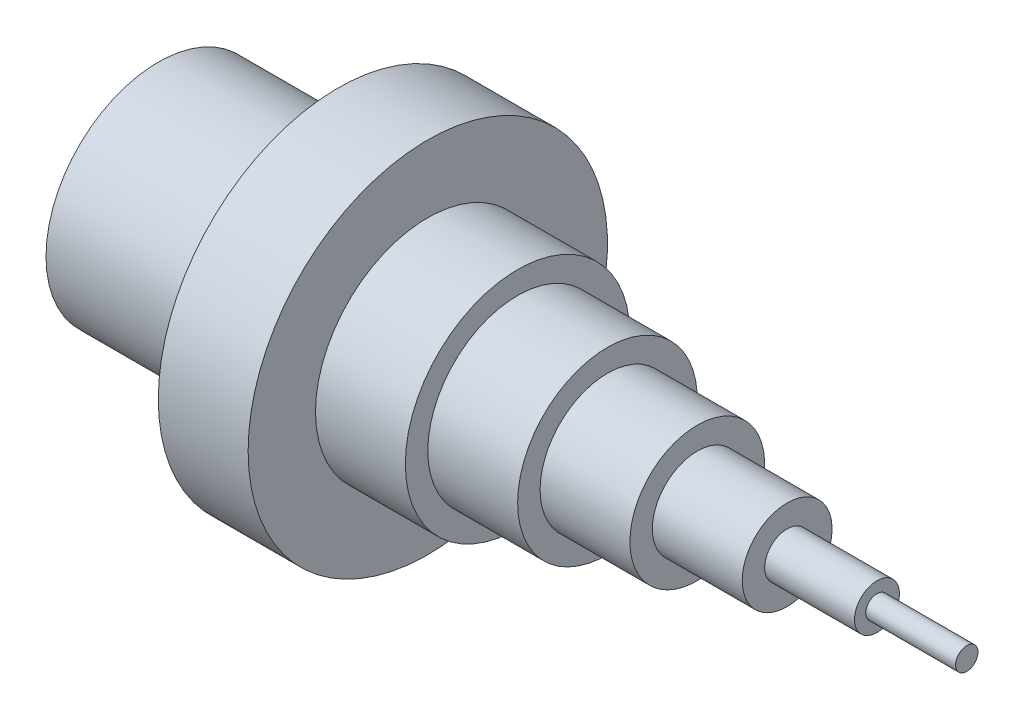
SolidWorks part; units mm, degrees
ref_plane "Front Plane" through (0, 0, 0) normal (0, 0, 1) x (1, 0, 0)
ref_plane "Top Plane" through (0, 0, 0) normal (0, 1, 0) x (1, 0, 0)
ref_plane "Right Plane" through (0, 0, 0) normal (1, 0, 0) x (0, 0, -1)
sketch "Sketch2" plane through (0, 0, 0) normal (0, 1, 0) x (1, 0, 0)
  line L0 (0, 0) -> (183.4043, 0) construction
  line L1 (0, 0) -> (0, -25)
  line L2 (0, -25) -> (40, -25)
  line L3 (40, -25) -> (40, -40)
  line L4 (40, -40) -> (60, -40)
  line L5 (60, -40) -> (60, -25)
  line L6 (60, -25) -> (80, -25)
  line L7 (80, -25) -> (80, -20)
  line L8 (80, -20) -> (100, -20)
  line L9 (100, -20) -> (100, -15)
  line L10 (100, -15) -> (120, -15)
  line L11 (120, -15) -> (120, -10)
  line L12 (120, -10) -> (140, -10)
  line L13 (140, -10) -> (140, -5)
  line L14 (140, -5) -> (160, -5)
  line L15 (160, -5) -> (160, -2.5)
  line L16 (160, -2.5) -> (180, -2.5)
  line L17 (180, -2.5) -> (180, 0)
  line L18 (0, 0) -> (180, 0)
  dimension "D1" = 20
  dimension "D2" = 20
  dimension "D3" = 20
  dimension "D4" = 20
  dimension "D5" = 20
  dimension "D6" = 20
  dimension "D7" = 20
  dimension "D8" = 5
  dimension "D9" = 10
  dimension "D10" = 20
  dimension "D11" = 30
  dimension "D12" = 40
  dimension "D13" = 50
  dimension "D14" = 50
  dimension "D15" = 80
  dimension "D16" = 40
revolve "Revolve1" add sketch "Sketch2" angle 360 about L0
sketch "Sketch3" plane through (0, 0, 0) normal (-1, 0, 0) x (0, 0, 1)
  circle A0 centre (0, 0) radius 20
  dimension "D1" = 40
extrude "Cut-Extrude1" cut sketch "Sketch3" against normal blind 40
